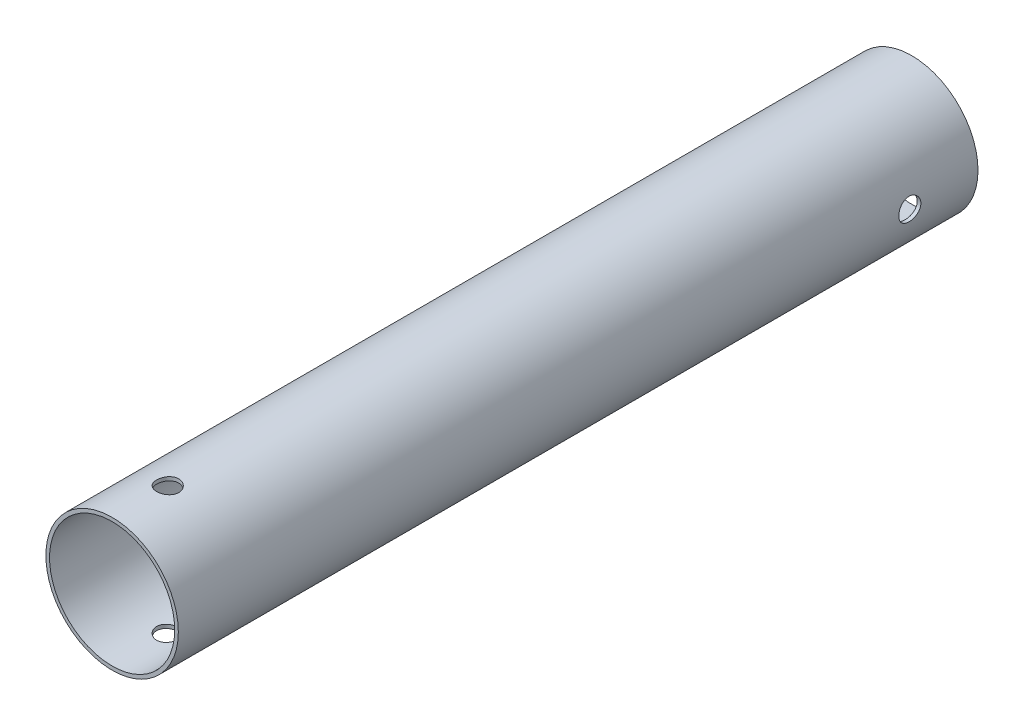
SolidWorks part; units mm, degrees
material "6061-O (SS)"
ref_plane "Alzado" through (0, 0, 0) normal (0, 0, 1) x (1, 0, 0)
ref_plane "Planta" through (0, 0, 0) normal (0, 1, 0) x (1, 0, 0)
ref_plane "Vista lateral" through (0, 0, 0) normal (1, 0, 0) x (0, 0, -1)
sketch "Croquis1" plane through (0, 0, 0) normal (0, 0, 1) x (1, 0, 0)
  circle A0 centre (0, 0) radius 9.525
  circle A1 centre (0, 0) radius 9
  dimension "D1" = 19.05
  dimension "D2" = 18
extrude "Saliente-Extruir1" add sketch "Croquis1" along normal blind 115
sketch "Croquis2" plane through (0, 0, 0) normal (1, 0, 0) x (0, 0, -1)
  line L0 (0, 0) -> (-115, 0) construction
  line L1 (-115, 9.525) -> (-115, -9.525) construction
  line L2 (0, -9) -> (0, 9) construction
  circle A0 centre (-9.8, 0) radius 1.5875
  dimension "D1" = 3.175
  dimension "D2" = 9.8
extrude "Cortar-Extruir1" cut sketch "Croquis2" against normal through all both and the other way through all
sketch "Croquis3" plane through (0, 0, 0) normal (0, 1, 0) x (1, 0, 0)
  line L0 (0, 0) -> (0, -115) construction
  line L1 (-9.525, -115) -> (9.525, -115) construction
  circle A0 centre (0, -107.0025) radius 1.5875
  point P9 (0, -110.0775)
  dimension "D1" = 3.175
  dimension "D2" = 6.41
extrude "Cortar-Extruir2" cut sketch "Croquis3" against normal through all both and the other way through all
